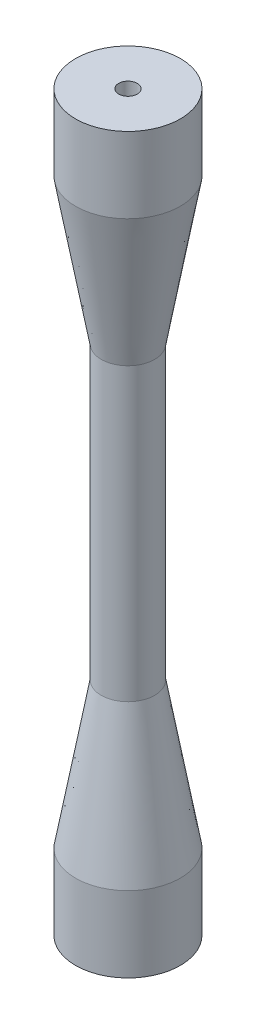
SolidWorks part; units mm, degrees
ref_plane "Front Plane" through (0, 0, 0) normal (0, 0, 1) x (1, 0, 0)
ref_plane "Top Plane" through (0, 0, 0) normal (0, 1, 0) x (1, 0, 0)
ref_plane "Right Plane" through (0, 0, 0) normal (1, 0, 0) x (0, 0, -1)
sketch "Sketch1" plane through (0, 0, 0) normal (0, 1, 0) x (1, 0, 0)
  circle A0 centre (0, 0) radius 9
  circle A1 centre (0, 0) radius 1.6
  dimension "D1" = 3.2
  dimension "D2" = 18
extrude "Boss-Extrude1" add sketch "Sketch1" along normal blind 3
sketch "Sketch2" plane through (0, 0, 0) normal (0, -1, 0) x (1, 0, 0)
  line L0 (0, 5) -> (-7.4833, 5)
  line L1 (0, -5) -> (-7.4833, -5)
  circle A0 centre (0, 0) radius 5
  circle A1 centre (0, 0) radius 9 construction
  arc A2 (-7.4833, 5) -> (-7.4833, -5) centre (0, 0) cw
  circle M1 centre (0, 0) radius 9
extrude "Boss-Extrude2" add sketch "Sketch2" along normal blind 10 contours A0 L1 L0 M1
sketch "Sketch3" plane through (0, -10, 0) normal (0, -1, 0) x (1, 0, 0)
  circle A0 centre (0, 0) radius 9
extrude "Boss-Extrude3" add sketch "Sketch3" along normal blind 25 draft 10
sketch "Sketch4" plane through (0, -35, 0) normal (0, -1, 0) x (1, 0, 0)
  circle A0 centre (0, 0) radius 4.5918
extrude "Boss-Extrude4" add sketch "Sketch4" along normal blind 25
mirror "Mirror2" about plane through (0, -60, 0) normal (0, -1, 0) of "Boss-Extrude2", "Boss-Extrude4", "Boss-Extrude3", "Boss-Extrude1"
